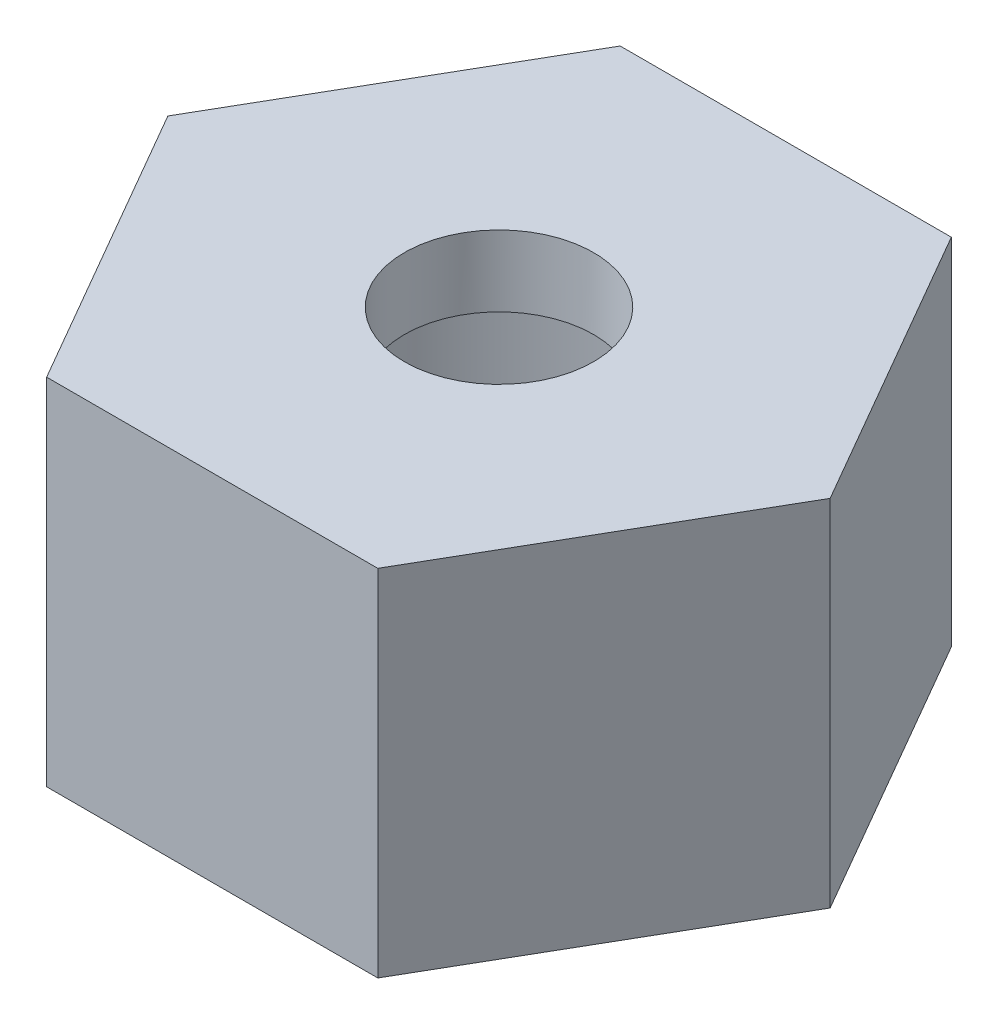
SolidWorks part; units mm, degrees
ref_plane "Front Plane" through (0, 0, 0) normal (0, 0, 1) x (1, 0, 0)
ref_plane "Top Plane" through (0, 0, 0) normal (0, 1, 0) x (1, 0, 0)
ref_plane "Right Plane" through (0, 0, 0) normal (1, 0, 0) x (0, 0, -1)
sketch "Sketch1" plane through (0, 0, 0) normal (0, 1, 0) x (1, 0, 0)
  line L1 (-14, 0) -> (-7, -12.1244)
  line L2 (-7, -12.1244) -> (7, -12.1244)
  line L3 (7, -12.1244) -> (14, 0)
  line L4 (14, 0) -> (7, 12.1244)
  line L5 (7, 12.1244) -> (-7, 12.1244)
  line L6 (-7, 12.1244) -> (-14, 0)
  circle A0 centre (0, 0) radius 12.1244 construction
  point P1 (0, 0)
  dimension "D1" = 14
extrude "Boss-Extrude1" add sketch "Sketch1" along normal mid plane 15
sketch "Sketch2" plane through (0, -7.5, 0) normal (0, -1, 0) x (1, 0, 0)
  circle A0 centre (0, 0) radius 10
  dimension "D1" = 20
extrude "Cut-Extrude2" cut sketch "Sketch2" against normal blind 12
sketch "Sketch3" plane through (0, 7.5, 0) normal (0, 1, 0) x (1, 0, 0)
  circle A0 centre (0, 0) radius 4
  dimension "D1" = 8
extrude "Cut-Extrude3" cut sketch "Sketch3" against normal through all
